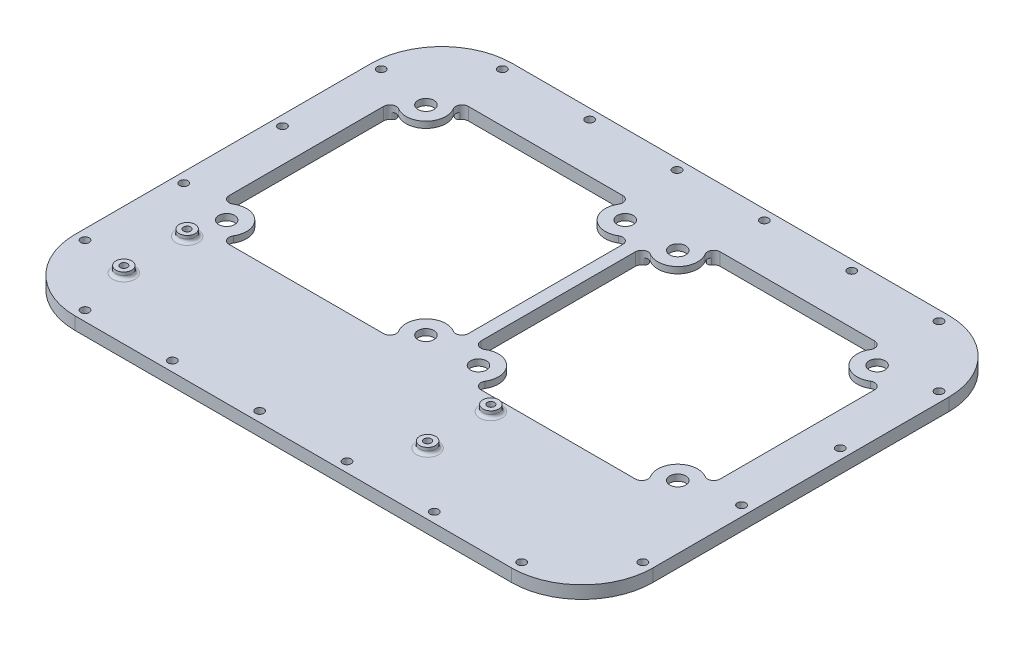
SolidWorks part; units mm, degrees
ref_plane "Front Plane" through (0, 0, 0) normal (0, 0, 1) x (1, 0, 0)
ref_plane "Top Plane" through (0, 0, 0) normal (0, 1, 0) x (1, 0, 0)
ref_plane "Right Plane" through (0, 0, 0) normal (1, 0, 0) x (0, 0, -1)
sketch "Sketch1" plane through (0, 0, 0) normal (0, 1, 0) x (1, 0, 0)
  line L0 (-64.7625, 33.175) -> (-61.5875, 30) construction
  line L1 (-61.5875, -30) -> (-1.5875, -30) construction
  line L2 (-61.5875, -30) -> (-61.5875, 30) construction
  line L3 (-61.5875, 30) -> (-1.5875, 30) construction
  line L4 (-1.5875, -30) -> (-1.5875, 30) construction
  line L5 (-61.5875, -30) -> (-1.5875, 30) construction
  line L6 (-61.5875, 30) -> (-1.5875, -30) construction
  line L7 (-6.5875, -25) -> (-56.5875, -25) construction
  line L8 (-6.5875, -25) -> (-6.5875, 25) construction
  line L9 (-6.5875, 25) -> (-56.5875, 25) construction
  line L10 (-56.5875, -25) -> (-56.5875, 25) construction
  line L11 (-6.5875, -25) -> (-56.5875, 25) construction
  line L12 (-6.5875, 25) -> (-56.5875, -25) construction
  line L13 (64.7625, -33.175) -> (-64.7625, -33.175)
  line L14 (64.7625, -33.175) -> (64.7625, 33.175)
  line L15 (64.7625, 33.175) -> (-64.7625, 33.175)
  line L16 (-64.7625, -33.175) -> (-64.7625, 33.175)
  line L17 (64.7625, -33.175) -> (-64.7625, 33.175) construction
  line L18 (64.7625, 33.175) -> (-64.7625, -33.175) construction
  line L19 (-64.7625, -33.175) -> (-61.5875, -30) construction
  line L20 (-31.5875, 0) -> (31.5875, 0) construction
  line L22 (56.5875, -25) -> (6.5875, -25) construction
  line L23 (56.5875, -25) -> (56.5875, 25) construction
  line L24 (56.5875, 25) -> (6.5875, 25) construction
  line L25 (6.5875, -25) -> (6.5875, 25) construction
  line L26 (56.5875, -25) -> (6.5875, 25) construction
  line L27 (56.5875, 25) -> (6.5875, -25) construction
  circle A0 centre (-56.5875, 25) radius 2
  circle A1 centre (-6.5875, 25) radius 2
  circle A2 centre (-6.5875, -25) radius 2
  circle A3 centre (-56.5875, -25) radius 2
  circle A4 centre (6.5875, 25) radius 2
  circle A5 centre (56.5875, 25) radius 2
  circle A6 centre (56.5875, -25) radius 2
  circle A7 centre (6.5875, -25) radius 2
  point P0 (-31.5875, 0)
  point P5 (-31.5875, 0)
  point P14 (0, 0)
  point P22 (0, 0)
  dimension "D3" = 4
  dimension "D1" = 60
  dimension "D2" = 50
  dimension "D4" = 1.5875
  dimension "D5" = 3.175
extrude "Boss-Extrude1" add sketch "Sketch1" along normal blind 3.175
sketch "Sketch2" plane through (0, 0, 0) normal (0, 1, 0) x (1, 0, 0)
  line L0 (-56.5875, 25) -> (-6.5875, -25) construction
  line L1 (-31.5875, 0) -> (-31.5875, 30)
  line L2 (-31.5875, 30) -> (-50.9528, 30)
  line L3 (-61.5875, 19.3653) -> (-61.5875, 0)
  line L4 (-61.5875, 0) -> (-31.5875, 0)
  arc A0 (-52.3107, 27.5901) -> (-59.1776, 20.7232) centre (-56.5875, 25) cw
  arc A1 (-59.1776, 20.7232) -> (-61.5875, 19.3653) centre (-60, 19.3653) ccw
  arc A2 (-52.3107, 27.5901) -> (-50.9528, 30) centre (-50.9528, 28.4125) cw
  dimension "D1" = 1.5875
  dimension "D2" = 5
  dimension "D3" = 30
extrude "Cut-Extrude4" cut sketch "Sketch2" along normal through all
pattern_circular "CirPattern1" count 4 over 360 about axis through (-31.5875, 0, 0) along (0, 1, 0) of "Cut-Extrude4"
mirror "Mirror1" about plane through (0, 0, 0) normal (1, 0, 0) of "CirPattern1", "Cut-Extrude4"
sketch "Sketch4" plane through (0, 0, 33.175) normal (0, 0, 1) x (1, 0, 0)
  line L4 (-64.7625, 0) -> (64.7625, 0)
  line L5 (64.7625, 0) -> (64.7625, 3.175)
  line L6 (64.7625, 3.175) -> (-64.7625, 3.175)
  line L7 (-64.7625, 3.175) -> (-64.7625, 0)
  line L8 (-64.7625, 0) -> (64.7625, 0)
  line L9 (64.7625, 0) -> (64.7625, 3.175)
  line L10 (64.7625, 3.175) -> (-64.7625, 3.175)
  line L11 (-64.7625, 3.175) -> (-64.7625, 0)
  dimension "D1" = 0
extrude "Boss-Extrude2" add sketch "Sketch4" along normal blind 19.05
sketch "Sketch7" plane through (0, 3.175, 0) normal (0, 1, 0) x (1, 0, 0)
  line L0 (-61.5875, 19.3653) -> (-61.5875, -19.3653) construction
  line L1 (-58, -49.375) -> (18.2, -49.375) construction
  line L2 (-58, -49.375) -> (-58, -33.5) construction
  line L3 (-58, -33.5) -> (18.2, -33.5) construction
  line L4 (18.2, -49.375) -> (18.2, -33.5) construction
  line L5 (-58, -49.375) -> (18.2, -33.5) construction
  line L6 (-58, -33.5) -> (18.2, -49.375) construction
  line L8 (-58, -31.5) -> (18.2, -31.5) construction
  line L9 (-19.9, -31.5) -> (-19.9, 0) construction
  circle A0 centre (-58, -33.5) radius 2
  circle A1 centre (18.2, -33.5) radius 2
  circle A2 centre (18.2, -49.375) radius 2
  circle A3 centre (-58, -49.375) radius 2
  point P0 (-19.9, -41.4375)
  point P18 (-60, -33.5)
  dimension "D1" = 4
  dimension "D2" = 76.2
  dimension "D3" = 15.875
  dimension "D4" = 31.5
  dimension "D5" = 1.5875
extrude "Boss-Extrude3" add sketch "Sketch7" along normal blind 1.5875
sketch "Sketch9" plane through (0, 3.175, 0) normal (0, 1, 0) x (1, 0, 0)
  circle A0 centre (-58, -33.5) radius 0.9
  circle A1 centre (-58, -49.375) radius 0.9
  circle A2 centre (18.2, -49.375) radius 0.9
  circle A3 centre (18.2, -33.5) radius 0.9
  dimension "D1" = 1.8
extrude "Cut-Extrude5" cut sketch "Sketch9" against normal through all both and the other way through all
fillet "Fillet1" radius 0.7937 4 edges at (18.2, 3.175, 35.5) (18.2, 3.175, 51.375) (-58, 3.175, 51.375) (-58, 3.175, 35.5)
sketch "Sketch10" plane through (0, 0, 0) normal (0, -1, 0) x (1, 0, 0)
  circle A0 centre (56.5875, -25) radius 5.08
  circle A1 centre (56.5875, 25) radius 5.08
  circle A2 centre (6.5875, 25) radius 5.08
  circle A3 centre (6.5875, -25) radius 5.08
  circle A4 centre (-6.5875, -25) radius 5.08
  circle A5 centre (-6.5875, 25) radius 5.08
  circle A6 centre (-56.5875, 25) radius 5.08
  circle A7 centre (-56.5875, -25) radius 5.08
  dimension "D1" = 10.16
extrude "Cut-Extrude6" cut sketch "Sketch10" against normal blind 1.5875
fillet "Fillet2" radius 0.7937 16 edges at (3.5922, 0.7937, 20.897) (3.5922, 0.7937, -20.897) (10.6905, 0.7937, -27.9953) (52.4845, 0.7937, -27.9953) (59.5828, 0.7937, -20.897) (59.5828, 0.7937, 20.897) (52.4845, 0.7937, 27.9953) (10.6905, 0.7937, 27.9953) (-3.5922, 0.7937, 20.897) (-10.6905, 0.7937, 27.9953) (-59.5828, 0.7937, -20.897) (-52.4845, 0.7937, -27.9953) (-10.6905, 0.7937, -27.9953) (-3.5922, 0.7937, -20.897) (-59.5828, 0.7937, 20.897) (-52.4845, 0.7937, 27.9953)
sketch "Sketch11" plane through (0, 3.175, 0) normal (0, -1, 0) x (1, 0, 0)
  line L4 (-72.4687, 47.1475) -> (-72.4688, -27.1475)
  line L5 (-54.7687, -44.8475) -> (54.7688, -44.8475)
  line L6 (72.4688, -27.1475) -> (72.4688, 47.1475)
  line L7 (54.7688, 64.8475) -> (-54.7687, 64.8475)
  line L8 (-72.4687, 47.1475) -> (-72.4688, -27.1475)
  line L9 (-54.7687, -44.8475) -> (54.7688, -44.8475)
  line L10 (72.4688, -27.1475) -> (72.4688, 47.1475)
  line L11 (54.7688, 64.8475) -> (-54.7687, 64.8475)
  line L12 (-64.7625, 52.225) -> (-64.7625, -33.175)
  line L13 (-64.7625, -33.175) -> (64.7625, -33.175)
  line L14 (64.7625, -33.175) -> (64.7625, 52.225)
  line L15 (64.7625, 52.225) -> (-64.7625, 52.225)
  line L16 (-64.7625, 52.225) -> (-64.7625, -33.175)
  line L17 (-64.7625, -33.175) -> (64.7625, -33.175)
  line L18 (64.7625, -33.175) -> (64.7625, 52.225)
  line L19 (64.7625, 52.225) -> (-64.7625, 52.225)
  arc A4 (-54.7687, 64.8475) -> (-72.4687, 47.1475) centre (-54.7687, 47.1475) ccw
  arc A5 (-72.4688, -27.1475) -> (-54.7687, -44.8475) centre (-54.7687, -27.1475) ccw
  arc A6 (54.7688, -44.8475) -> (72.4688, -27.1475) centre (54.7688, -27.1475) ccw
  arc A7 (72.4688, 47.1475) -> (54.7688, 64.8475) centre (54.7688, 47.1475) ccw
  arc A8 (-54.7687, 64.8475) -> (-72.4687, 47.1475) centre (-54.7687, 47.1475) ccw
  arc A9 (-72.4688, -27.1475) -> (-54.7687, -44.8475) centre (-54.7687, -27.1475) ccw
  arc A10 (54.7688, -44.8475) -> (72.4688, -27.1475) centre (54.7688, -27.1475) ccw
  arc A11 (72.4688, 47.1475) -> (54.7688, 64.8475) centre (54.7688, 47.1475) ccw
  dimension "D1" = 0
  dimension "D2" = 0
extrude "Boss-Extrude4" add sketch "Sketch11" along normal up to surface (3.175 mm away) up to face at (18.2, 0, 34.4)
sketch "Sketch12" plane through (0, 0, 0) normal (0, -1, 0) x (1, 0, 0)
  circle A0 centre (54.7688, -42.3475) radius 1.05
  circle A1 centre (32.8612, -42.3475) radius 1.05
  circle A2 centre (10.9537, -42.3475) radius 1.05
  circle A3 centre (69.9688, -27.1475) radius 1.05
  circle A4 centre (69.9688, -2.3825) radius 1.05
  point P15 (69.9688, -27.1475)
  point P17 (69.9688, -2.3825)
  point P19 (54.7688, -42.3475)
  point P21 (32.8612, -42.3475)
  point P23 (10.9537, -42.3475)
  dimension "D1" = 2.1
extrude "Cut-Extrude7" cut sketch "Sketch12" against normal through all
sketch "Sketch13" plane through (0, 0, 0) normal (0, -1, 0) x (1, 0, 0)
  circle A0 centre (69.9688, -27.1475) radius 1.875
  circle A1 centre (69.9688, -2.3825) radius 1.875
  circle A2 centre (54.7688, -42.3475) radius 1.875
  circle A3 centre (32.8612, -42.3475) radius 1.875
  circle A4 centre (10.9537, -42.3475) radius 1.875
  dimension "D1" = 3.75
extrude "Cut-Extrude8" cut sketch "Sketch13" against normal offset from surface (1.675 mm away) 1.5 up to face at (69.9688, 3.175, -1.3325)
ref_plane "Plane1" through (0, 0, 10) normal (0, 0, -1) x (-1, 0, 0)
ref_plane "Plane2" through (0, 0, 0) normal (1, 0, 0) x (0, 0, -1)
mirror "Mirror2" about plane through (0, 0, 10) normal (0, 0, -1) of "Cut-Extrude8", "Cut-Extrude7"
mirror "Mirror3" about plane through (0, 0, 0) normal (1, 0, 0) of "Mirror2", "Cut-Extrude7", "Cut-Extrude8"
